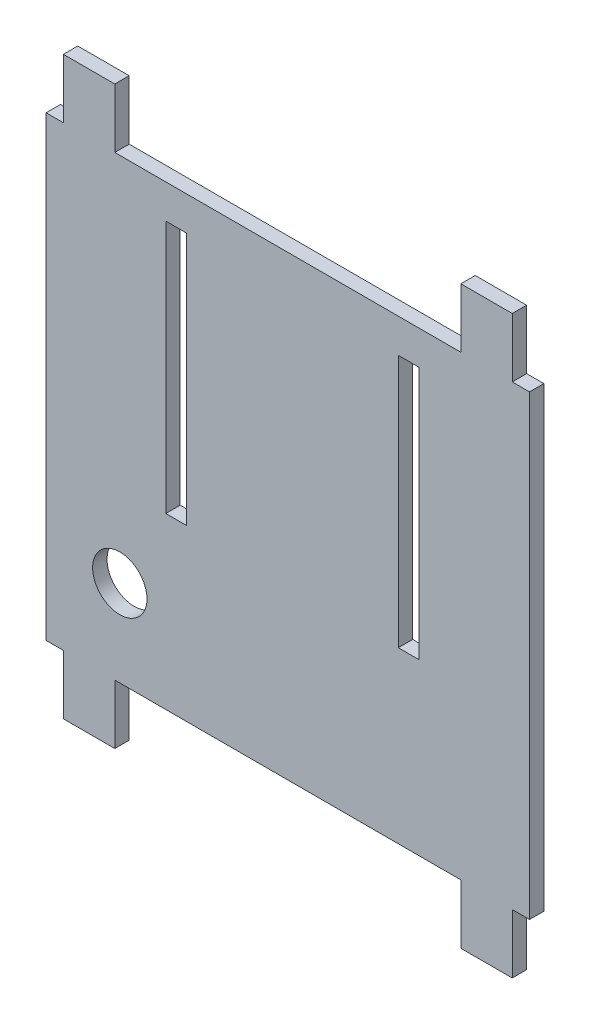
SolidWorks part; units mm, degrees
ref_plane "Front Plane" through (0, 0, 0) normal (0, 0, 1) x (1, 0, 0)
ref_plane "Top Plane" through (0, 0, 0) normal (0, 1, 0) x (1, 0, 0)
ref_plane "Right Plane" through (0, 0, 0) normal (1, 0, 0) x (0, 0, -1)
sketch "Sketch1" plane through (0, 0, 0) normal (0, 0, 1) x (1, 0, 0)
  line L1 (-38.1783, 79.4872) -> (68.5017, 79.4872)
  line L2 (-38.1783, 79.4872) -> (-38.1783, -47.5128)
  line L3 (-38.1783, -47.5128) -> (68.5017, -47.5128)
  line L4 (68.5017, 79.4872) -> (68.5017, -47.5128)
extrude "Boss-Extrude1" add sketch "Sketch1" along normal blind 3.175
sketch "Sketch2" plane through (0, 0, 3.175) normal (0, 0, 1) x (1, 0, 0)
  line L0 (-38.1783, 79.4872) -> (-38.1783, -47.5128) construction
  line L1 (-11.7623, 58.9132) -> (-7.1903, 58.9132)
  line L2 (-11.7623, 58.9132) -> (-11.7623, 3.0332)
  line L3 (-11.7623, 3.0332) -> (-7.1903, 3.0332)
  line L4 (-7.1903, 58.9132) -> (-7.1903, 3.0332)
  line L5 (39.5457, 58.9132) -> (44.1177, 58.9132)
  line L6 (39.5457, 58.9132) -> (39.5457, 3.0332)
  line L7 (39.5457, 3.0332) -> (44.1177, 3.0332)
  line L8 (44.1177, 58.9132) -> (44.1177, 3.0332)
  line L9 (68.5017, 79.4872) -> (-38.1783, 79.4872) construction
  point P8 (44.1177, 30.9732)
  dimension "D1" = 51.308
  dimension "D2" = 26.416
  dimension "D3" = 4.572
  dimension "D4" = 55.88
  dimension "D5" = 20.574
extrude "Cut-Extrude1" cut sketch "Sketch2" against normal blind 3.175
sketch "Sketch3" plane through (0, 0, 3.175) normal (0, 0, 1) x (1, 0, 0)
  line L0 (68.5017, 79.4872) -> (-38.1783, 79.4872) construction
  line L1 (-38.1783, 79.4872) -> (-34.3683, 79.4872)
  line L2 (-38.1783, 79.4872) -> (-38.1783, 66.4072)
  line L3 (-38.1783, 66.4072) -> (-34.3683, 66.4072)
  line L4 (-34.3683, 79.4872) -> (-34.3683, 66.4072)
  line L5 (-23.0183, 79.4872) -> (53.3417, 79.4872)
  line L6 (-23.0183, 79.4872) -> (-23.0183, 66.4072)
  line L7 (-23.0183, 66.4072) -> (53.3417, 66.4072)
  line L8 (53.3417, 79.4872) -> (53.3417, 66.4072)
  line L9 (-38.1783, -34.4328) -> (-34.3683, -34.4328)
  line L10 (68.5017, 79.4872) -> (64.6917, 79.4872)
  line L11 (68.5017, 79.4872) -> (68.5017, 66.4072)
  line L12 (68.5017, 66.4072) -> (64.6917, 66.4072)
  line L13 (64.6917, 79.4872) -> (64.6917, 66.4072)
  line L14 (-38.1783, -34.4328) -> (-38.1783, -47.5128)
  line L15 (-38.1783, -47.5128) -> (-34.3683, -47.5128)
  line L16 (-34.3683, -34.4328) -> (-34.3683, -47.5128)
  line L17 (-23.0183, -34.4328) -> (53.3417, -34.4328)
  line L18 (-23.0183, -34.4328) -> (-23.0183, -47.5128)
  line L19 (-23.0183, -47.5128) -> (53.3417, -47.5128)
  line L20 (53.3417, -34.4328) -> (53.3417, -47.5128)
  line L21 (68.5017, -34.4328) -> (64.6917, -34.4328)
  line L22 (68.5017, -34.4328) -> (68.5017, -47.5128)
  line L23 (68.5017, -47.5128) -> (64.6917, -47.5128)
  line L24 (64.6917, -34.4328) -> (64.6917, -47.5128)
  line L26 (-38.1783, -47.5128) -> (68.5017, -47.5128) construction
  line L28 (-38.1783, 79.4872) -> (-38.1783, -47.5128) construction
  line L29 (68.5017, -47.5128) -> (68.5017, 79.4872) construction
  dimension "D1" = 11.35
  dimension "D2" = 11.35
  dimension "D3" = 3.81
  dimension "D4" = 11.35
  dimension "D5" = 11.35
  dimension "D6" = 13.08
  dimension "D7" = 3.81
  dimension "D8" = 3.81
  dimension "D9" = 76.36
extrude "Cut-Extrude2" cut sketch "Sketch3" against normal blind 3.175
sketch "Sketch4" plane through (0, 0, 3.175) normal (0, 0, 1) x (1, 0, 0)
  line L0 (-38.1783, 66.4072) -> (-38.1783, -34.4328) construction
  line L1 (53.3417, -34.4328) -> (-23.0183, -34.4328) construction
  circle A0 centre (-21.9096, -15.3828) radius 6
  dimension "D1" = 16.2687
  dimension "D2" = 19.05
extrude "Cut-Extrude3" cut sketch "Sketch4" against normal blind 3.175
